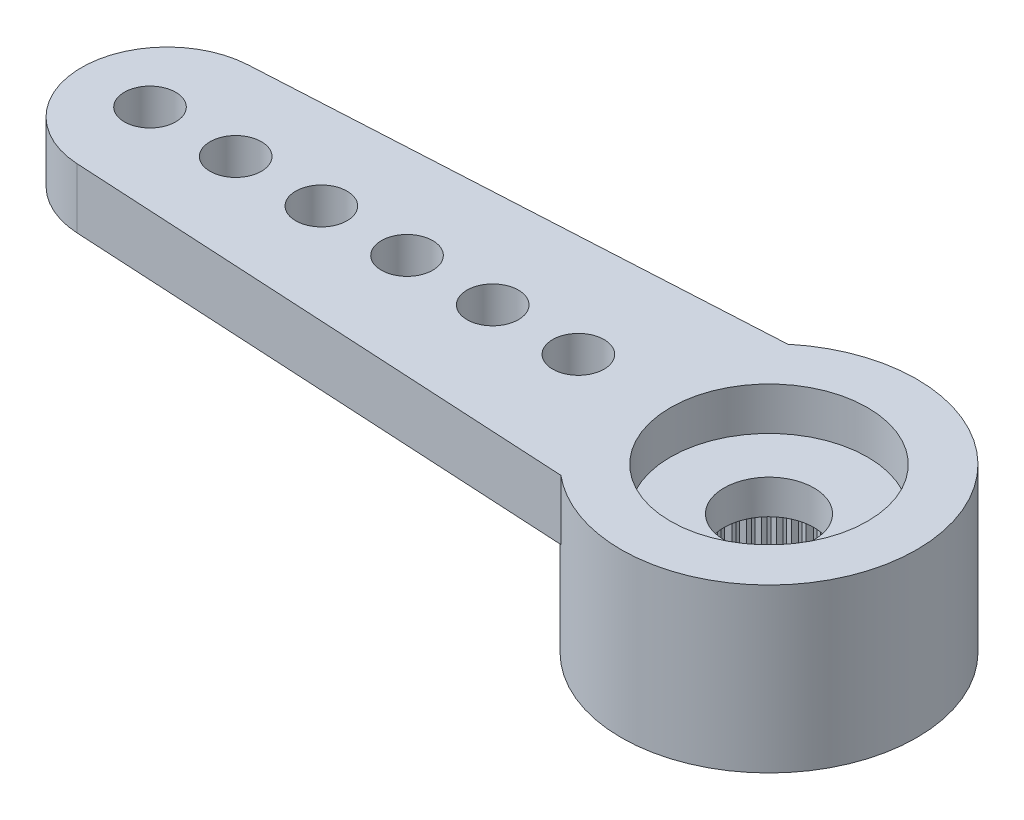
SolidWorks part; units mm, degrees
material "PVC Rígido"
ref_plane "Plano frontal" through (0, 0, 0) normal (0, 0, 1) x (1, 0, 0)
ref_plane "Plano superior" through (0, 0, 0) normal (0, 1, 0) x (1, 0, 0)
ref_plane "Plano direito" through (0, 0, 0) normal (1, 0, 0) x (0, 0, -1)
sketch "Esboço1" plane through (0, 0, 0) normal (0, 1, 0) x (1, 0, 0)
  line L0 (0, 0) -> (-14.05, 0) construction
  line L1 (-14.1591, 1.997) -> (-2.2091, 2.65)
  line L2 (-2.2091, -2.65) -> (-14.1591, -1.997)
  arc A0 (-2.2091, -2.65) -> (-2.2091, 2.65) centre (0, 0) ccw
  arc A1 (-14.1591, 1.997) -> (-14.1591, -1.997) centre (-14.05, 0) ccw
  dimension "D1" = 6.9
  dimension "D2" = 4
  dimension "D3" = 19.5
  dimension "D4" = 5.3
extrude "Ressalto-extrusão1" add sketch "Esboço1" against normal blind 1.4
sketch "Esboço2" plane through (0, -1.4, 0) normal (0, -1, 0) x (1, 0, 0)
  arc A0 (-2.2091, -2.65) -> (-2.2091, 2.65) centre (0, 0) ccw construction
  circle A1 centre (0, 0) radius 3.45
extrude "Ressalto-extrusão2" add sketch "Esboço2" along normal offset from surface (2.4 mm away) 3.8 up to face at (-7.242, 0, 0)
hole_wizard "Furo4" positions "Esboço9" profile "Esboço10" legacy end condition through all
sketch "Esboço9" plane through (0, 0, 0) normal (0, 1, 0) x (1, 0, 0)
  line L1 (-14.45, 0) -> (0, 0) construction
  arc A2 (-14.1591, 1.997) -> (-14.1591, -1.997) centre (-14.05, 0) ccw construction
  point P0 (-14.45, 0)
  point P19 (-16.05, 0)
  dimension "D1" = 1.6
sketch "Esboço10" plane through (-14.45, 0, 0) normal (1, 0, 0) x (0, 0, 1)
  line L0 (0, 0) -> (0, 3.8)
  line L1 (0, 3.8) -> (0.6, 3.8)
  line L2 (0.6, 3.8) -> (0.6, 0)
  line L3 (0.6, 0) -> (0, 0)
  line L4 (0, 110) -> (0, -10) construction
  dimension "Diameter" = 1.2
  dimension "Depth" = 3.8
pattern_linear "Padrão linear1" count 6 spacing 2 along (1, 0, 0) of "Furo4"
hole_wizard "Furo1" positions "Esboço3" profile "Esboço4" legacy
sketch "Esboço3" plane through (0, -3.8, 0) normal (0, -1, 0) x (-1, 0, 0)
  point P0 (0, 0)
sketch "Esboço4" plane through (0, -3.8, 0) normal (1, 0, 0) x (0, 0, -1)
  line L0 (0, 0) -> (0, 2)
  line L1 (0, 2) -> (2.475, 2)
  line L2 (2.475, 2) -> (2.475, 0)
  line L3 (2.475, 0) -> (0, 0)
  line L4 (0, 110) -> (0, -10) construction
  dimension "Diameter" = 4.95
  dimension "Depth" = 2
hole_wizard "Furo2" positions "Esboço5" profile "Esboço6" legacy
sketch "Esboço5" plane through (0, 0, 0) normal (0, 1, 0) x (1, 0, 0)
  point P0 (0, 0)
sketch "Esboço6" plane through (0, 0, 0) normal (1, 0, 0) x (0, 0, 1)
  line L0 (0, 0) -> (0, 1)
  line L1 (0, 1) -> (2.3, 1)
  line L2 (2.3, 1) -> (2.3, 0)
  line L3 (2.3, 0) -> (0, 0)
  line L4 (0, 110) -> (0, -10) construction
  dimension "Diameter" = 4.6
  dimension "Depth" = 1
hole_wizard "Furo3" positions "Esboço7" profile "Esboço8" legacy end condition through all
sketch "Esboço7" plane through (0, 0, 0) normal (0, 1, 0) x (1, 0, 0)
  point P0 (0, 0)
sketch "Esboço8" plane through (0, 0, 0) normal (1, 0, 0) x (0, 0, 1)
  line L0 (0, 0) -> (0, 3.8)
  line L1 (0, 3.8) -> (1.05, 3.8)
  line L2 (1.05, 3.8) -> (1.05, 0)
  line L3 (1.05, 0) -> (0, 0)
  line L4 (0, 110) -> (0, -10) construction
  dimension "Diameter" = 2.1
  dimension "Depth" = 3.8
sketch "Esboço11" plane through (0, -3.8, 0) normal (0, -1, 0) x (1, 0, 0)
  line L0 (-0.0981, 2.4731) -> (0, 2.375)
  line L1 (0, 2.375) -> (0.0981, 2.4731)
  line L2 (0, 0) -> (0, 2.475) construction
  circle A0 centre (0, 0) radius 2.375 construction
  circle A1 centre (0, 0) radius 2.475
  arc A2 (0.0981, 2.4731) -> (-0.0981, 2.4731) centre (0, 0) ccw
  dimension "D3" = 4.75
  dimension "D2" = 0.1
  dimension "D1" = 0
extrude "Ressalto-extrusão3" add sketch "Esboço11" against normal up to surface (2 mm away) up to face at (0, -1.8, 1.05)
pattern_circular "PadrãoCircular1" count 60 over 360 about axis through (0, 0, 0) along (0, 1, 0) of "Ressalto-extrusão3"
sketch "Sketch1" plane through (0, 0, 0) normal (0, 1, 0) x (1, 0, 0)
  line L0 (0, 0) -> (-14.45, 0) construction
